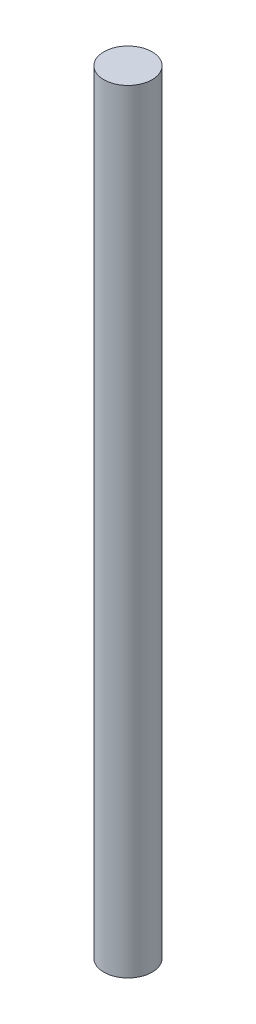
SolidWorks part; units mm, degrees
ref_plane "Front Plane" through (0, 0, 0) normal (0, 0, 1) x (1, 0, 0)
ref_plane "Top Plane" through (0, 0, 0) normal (0, 1, 0) x (1, 0, 0)
ref_plane "Right Plane" through (0, 0, 0) normal (1, 0, 0) x (0, 0, -1)
sketch "Çizim1" plane through (0, 0, 0) normal (0, 1, 0) x (1, 0, 0)
  circle A0 centre (0, 0) radius 100
extrude "Yükseklik-Ekstrüzyon1" add sketch "Çizim1" along normal blind 3200
